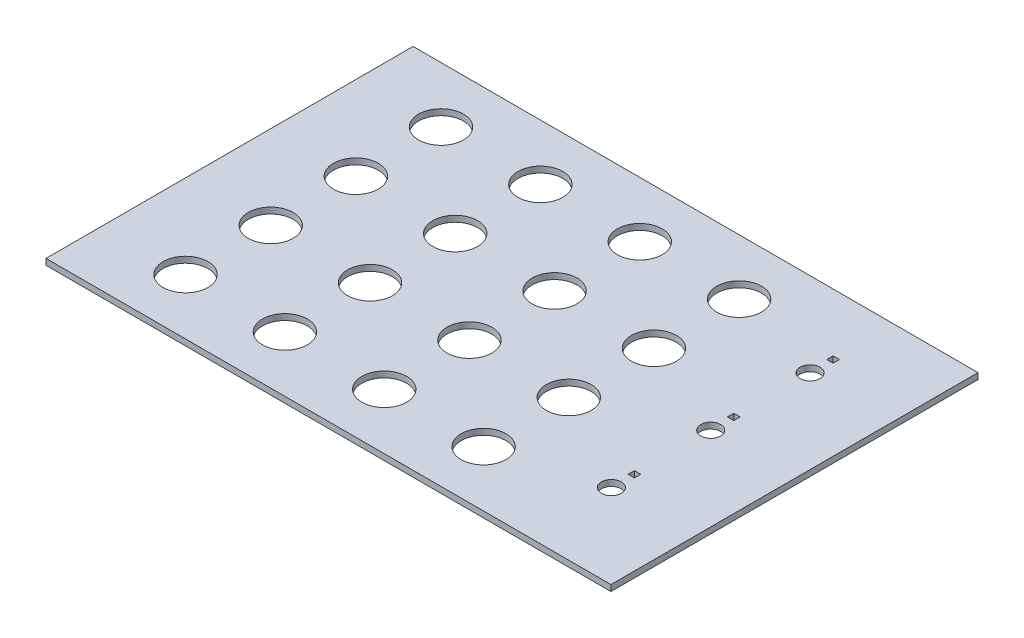
SolidWorks part; units mm, degrees
ref_plane "Front Plane" through (0, 0, 0) normal (0, 0, 1) x (1, 0, 0)
ref_plane "Top Plane" through (0, 0, 0) normal (0, 1, 0) x (1, 0, 0)
ref_plane "Right Plane" through (0, 0, 0) normal (1, 0, 0) x (0, 0, -1)
sketch "Sketch1" plane through (0, 0, 0) normal (0, 1, 0) x (1, 0, 0)
  line L0 (-70, 86.9805) -> (-70, -106.8016) construction
  line L1 (99.5, 64.65) -> (-99.5, 64.65)
  line L2 (99.5, 64.65) -> (99.5, -64.65)
  line L3 (99.5, -64.65) -> (-99.5, -64.65)
  line L4 (-99.5, 64.65) -> (-99.5, -64.65)
  line L5 (99.5, 64.65) -> (-99.5, -64.65) construction
  line L6 (99.5, -64.65) -> (-99.5, 64.65) construction
  line L7 (0, 64.65) -> (0, -64.65) construction
  line L8 (-99.5, 0) -> (99.5, 0) construction
  line L9 (-70, 45) -> (-35, 45) construction
  line L10 (60.6732, 35) -> (77.1303, 35) construction
  line L11 (68.875, 44.25) -> (71.125, 44.25)
  line L12 (68.875, 44.25) -> (68.875, 42)
  line L13 (68.875, 42) -> (71.125, 42)
  line L14 (71.125, 44.25) -> (71.125, 42)
  line L15 (68.875, 44.25) -> (71.125, 42) construction
  line L16 (68.875, 42) -> (71.125, 44.25) construction
  line L17 (68.875, 9.25) -> (68.875, 7)
  line L18 (68.875, 9.25) -> (71.125, 9.25)
  line L19 (71.125, 9.25) -> (71.125, 7)
  line L20 (68.875, 7) -> (71.125, 7)
  line L21 (68.875, -25.75) -> (68.875, -28)
  line L22 (68.875, -25.75) -> (71.125, -25.75)
  line L23 (71.125, -25.75) -> (71.125, -28)
  line L24 (68.875, -28) -> (71.125, -28)
  circle A0 centre (-70, 45) radius 7.9
  circle A1 centre (-35, 45) radius 7.9
  circle A2 centre (0, 45) radius 7.9
  circle A3 centre (35, 45) radius 7.9
  circle A4 centre (-35, 15) radius 7.9
  circle A5 centre (0, 15) radius 7.9
  circle A6 centre (35, 15) radius 7.9
  circle A7 centre (-35, -15) radius 7.9
  circle A8 centre (0, -15) radius 7.9
  circle A9 centre (35, -15) radius 7.9
  circle A10 centre (-35, -45) radius 7.9
  circle A11 centre (0, -45) radius 7.9
  circle A12 centre (35, -45) radius 7.9
  circle A13 centre (-70, 15) radius 7.9
  circle A14 centre (-70, -15) radius 7.9
  circle A15 centre (-70, -45) radius 7.9
  circle A16 centre (70, 35) radius 3.5
  circle A17 centre (70, 0) radius 3.5
  circle A18 centre (70, -35) radius 3.5
  point P0 (0, 0)
  point P14 (70, 43.125)
  dimension "D3" = 15.8
  dimension "D15" = 7
  dimension "D19" = 3
  dimension "D1" = 129.3
  dimension "D2" = 199
  dimension "D4" = 4
  dimension "D6" = 35
  dimension "D7" = 19.65
  dimension "D8" = 19.65
  dimension "D9" = 3
  dimension "D10" = 29.65
  dimension "D11" = 29.65
  dimension "D12" = 35
  dimension "D13" = 29.5
  dimension "D14" = 29.5
  dimension "D16" = 2.25
  dimension "D17" = 7
  dimension "D18" = 2.25
  dimension "D20" = 7
  dimension "D5" = 4
extrude "Boss-Extrude1" add sketch "Sketch1" along normal blind 2.13
